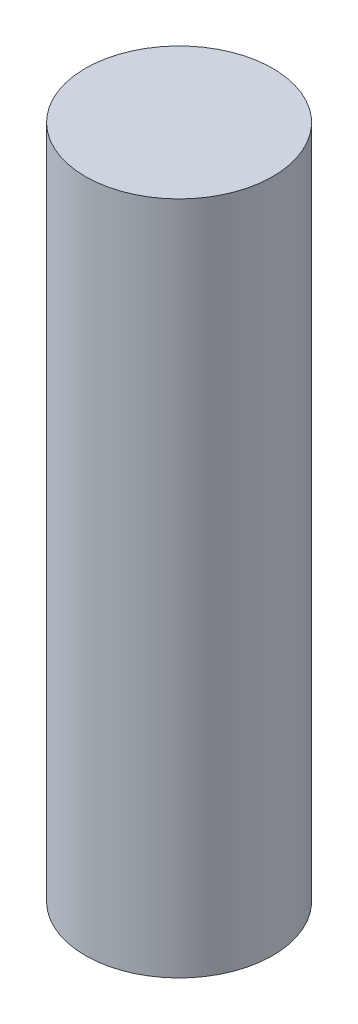
SolidWorks part; units mm, degrees
ref_plane "Front Plane" through (0, 0, 0) normal (0, 0, 1) x (1, 0, 0)
ref_plane "Top Plane" through (0, 0, 0) normal (0, 1, 0) x (1, 0, 0)
ref_plane "Right Plane" through (0, 0, 0) normal (1, 0, 0) x (0, 0, -1)
sketch "Sketch1" plane through (0, 0, 0) normal (0, 1, 0) x (1, 0, 0)
  circle A0 centre (0, 0) radius 2.5
  dimension "D1" = 5
extrude "Boss-Extrude1" add sketch "Sketch1" along normal blind 18
